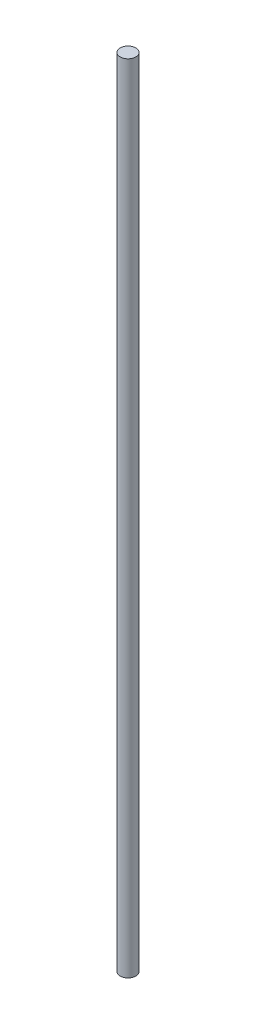
SolidWorks part; units mm, degrees
ref_plane "Front Plane" through (0, 0, 0) normal (0, 0, 1) x (1, 0, 0)
ref_plane "Top Plane" through (0, 0, 0) normal (0, 1, 0) x (1, 0, 0)
ref_plane "Right Plane" through (0, 0, 0) normal (1, 0, 0) x (0, 0, -1)
sketch "Sketch1" plane through (0, 0, 0) normal (0, 1, 0) x (1, 0, 0)
  circle A0 centre (0, 0) radius 4
  dimension "D1" = 8
extrude "Boss-Extrude1" add sketch "Sketch1" along normal blind 406
